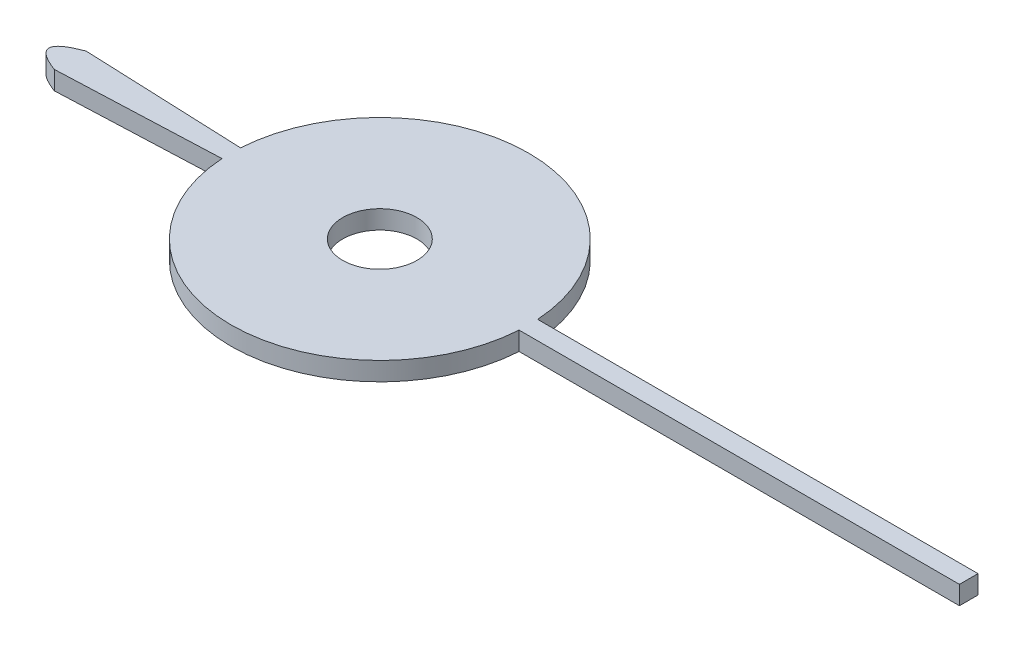
SolidWorks part; units mm, degrees
ref_plane "Front Plane" through (0, 0, 0) normal (0, 0, 1) x (1, 0, 0)
ref_plane "Top Plane" through (0, 0, 0) normal (0, 1, 0) x (1, 0, 0)
ref_plane "Right Plane" through (0, 0, 0) normal (1, 0, 0) x (0, 0, -1)
sketch "Sketch1" plane through (0, 0, 0) normal (0, 1, 0) x (1, 0, 0)
  line L0 (0, 0) -> (4, 0) construction
  line L1 (0, 0) -> (-0.3417, 0) construction
  line L2 (4, -0.25) -> (15.8593, -0.25)
  line L3 (4, 0.25) -> (15.8593, 0.25)
  line L4 (15.8593, 0.25) -> (15.8593, -0.25)
  line L5 (-8.9095, 0) -> (-0.1709, 0) construction
  line L6 (-8.3389, 0.4281) -> (-4, 0.25)
  line L7 (-8.3389, -0.4281) -> (-4, -0.25)
  circle A0 centre (0, 0) radius 4.0078
  spline S1 degree 2 poles (-8.3389, 0.4281) (-9.4802, 0) (-8.3389, -0.4281) knots 0 0 0 1 1 1
extrude "Boss-Extrude2" add sketch "Sketch1" along normal blind 0.5
sketch "Sketch3" plane through (0, 0.5, 0) normal (0, 1, 0) x (1, 0, 0)
  circle A0 centre (0, 0) radius 1
extrude "Cut-Extrude2" cut sketch "Sketch3" against normal through all
